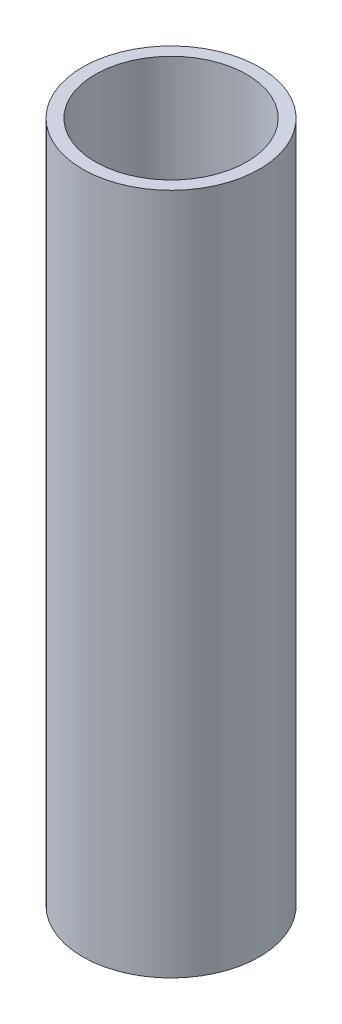
SolidWorks part; units mm, degrees
material "Silicon"
ref_plane "Front Plane" through (0, 0, 0) normal (0, 0, 1) x (1, 0, 0)
ref_plane "Top Plane" through (0, 0, 0) normal (0, 1, 0) x (1, 0, 0)
ref_plane "Right Plane" through (0, 0, 0) normal (1, 0, 0) x (0, 0, -1)
sketch "Sketch1" plane through (0, 0, 0) normal (0, 1, 0) x (1, 0, 0)
  circle A0 centre (0, 0) radius 38.1
  circle A1 centre (0, 0) radius 44.45
  dimension "D1" = 88.9
  dimension "D2" = 76.2
extrude "Boss-Extrude1" add sketch "Sketch1" along normal blind 342.9
